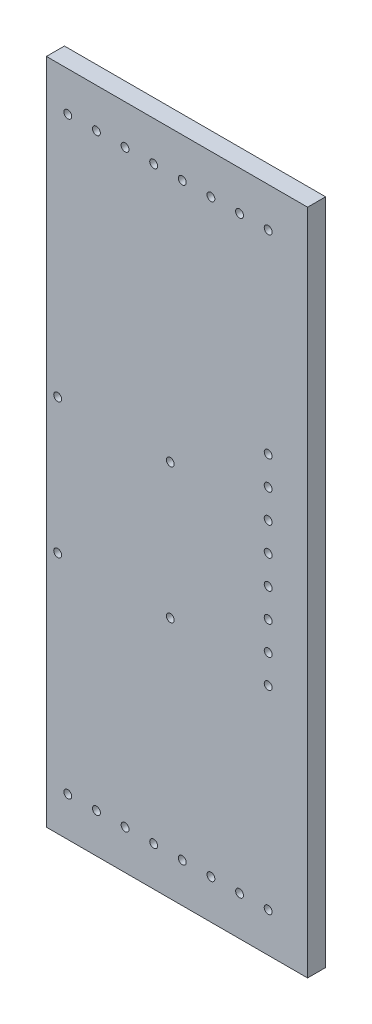
SolidWorks part; units mm, degrees
ref_plane "Plano frontal" through (0, 0, 0) normal (0, 0, 1) x (1, 0, 0)
ref_plane "Plano superior" through (0, 0, 0) normal (0, 1, 0) x (1, 0, 0)
ref_plane "Plano direito" through (0, 0, 0) normal (1, 0, 0) x (0, 0, -1)
sketch "Esboço1" plane through (0, 0, 0) normal (0, 0, 1) x (1, 0, 0)
  line L1 (-58, 148.25) -> (58, 148.25)
  line L2 (-58, 148.25) -> (-58, -148.25)
  line L3 (-58, -148.25) -> (58, -148.25)
  line L4 (58, 148.25) -> (58, -148.25)
  line L5 (-58, 148.25) -> (58, -148.25) construction
  line L6 (-58, -148.25) -> (58, 148.25) construction
  point P0 (0, 0)
  dimension "D1" = 296.5
  dimension "D2" = 116
extrude "Ressalto-extrusão1" add sketch "Esboço1" along normal blind 8
sketch "Esboço2" plane through (0, 0, 0) normal (0, 0, -1) x (-1, 0, 0)
  line L0 (58, -148.25) -> (-58, -148.25) construction
  line L2 (58, 148.25) -> (58, -148.25) construction
  circle A0 centre (3, -40.25) radius 1.75
  circle A1 centre (3, 19.75) radius 1.75
  circle A2 centre (53, 19.75) radius 1.75
  circle A3 centre (53, -40.25) radius 1.75
  dimension "D1" = 108
  dimension "D2" = 50
  dimension "D3" = 60
  dimension "D4" = 60
  dimension "D5" = 50
  dimension "D6" = 108
  dimension "D7" = 3.5
  dimension "D8" = 3.5
  dimension "D9" = 3.5
  dimension "D10" = 3.5
  dimension "D11" = 5
  dimension "D12" = 5
extrude "Corte-extrusão1" cut sketch "Esboço2" against normal blind 8
sketch "Esboço3" plane through (0, 0, 8) normal (0, 0, 1) x (1, 0, 0)
  line L0 (58, 148.25) -> (-58, 148.25) construction
  line L1 (-58, 148.25) -> (-58, -148.25) construction
  circle A0 centre (-48.5, 130.75) radius 1.75
  dimension "D1" = 17.5
  dimension "D2" = 9.5
  dimension "D3" = 3.5
extrude "Corte-extrusão2" cut sketch "Esboço3" against normal blind 100
pattern_linear "Padrão linear1" count 8 spacing 12.7143 along (1, 0, 0) count 2 spacing 261.5 along (0, -1, 0) of "Corte-extrusão2"
sketch "Esboço4" plane through (0, 0, 8) normal (0, 0, 1) x (1, 0, 0)
  line L0 (58, 148.25) -> (-58, 148.25) construction
  line L1 (58, -148.25) -> (58, 148.25) construction
  circle A0 centre (40.5, 44.5) radius 1.75
  dimension "D1" = 3.5
  dimension "D2" = 103.75
  dimension "D3" = 17.5
extrude "Corte-extrusão3" cut sketch "Esboço4" against normal blind 100
pattern_linear "Padrão linear2" count 8 spacing 12.7143 along (0, -1, 0) count 2 spacing 181.5 along (-1, 0, 0) of "Corte-extrusão3"
